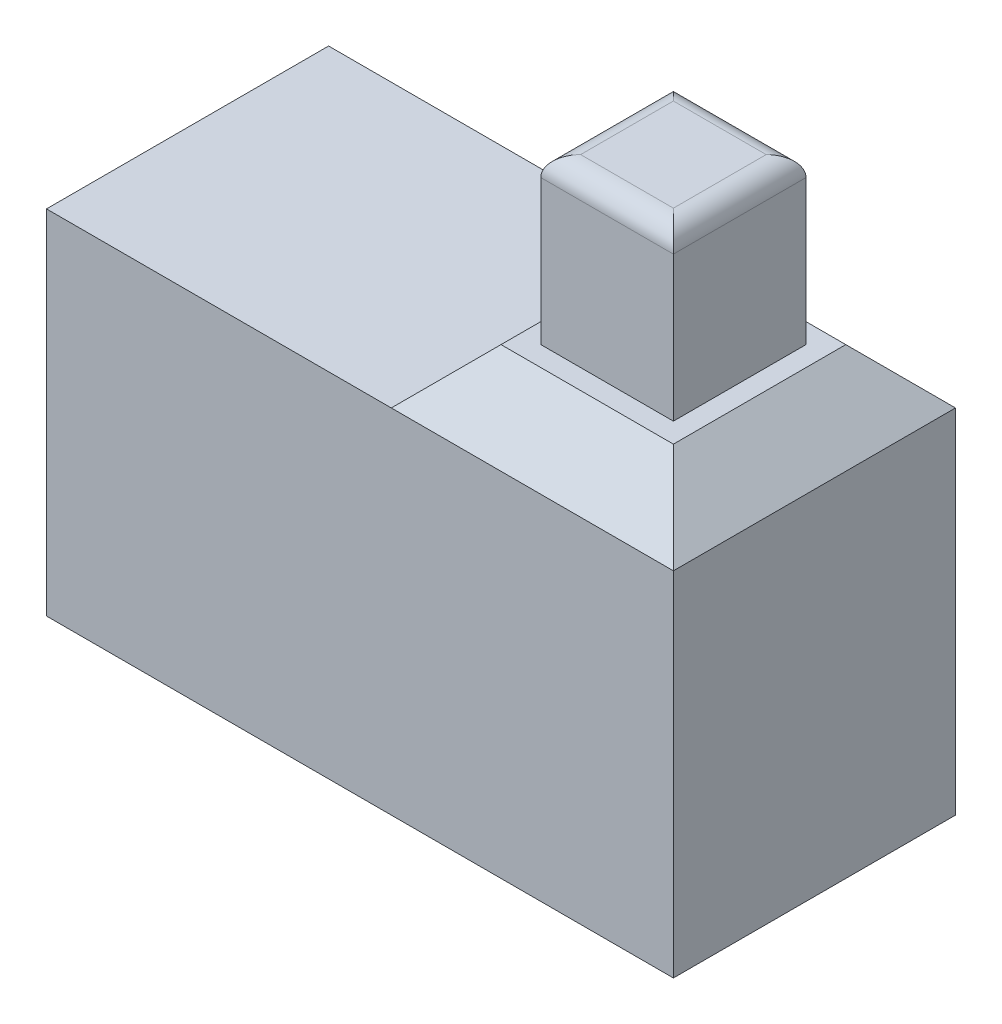
SolidWorks part; units mm, degrees
ref_plane "Front Plane" through (0, 0, 0) normal (0, 0, 1) x (1, 0, 0)
ref_plane "Top Plane" through (0, 0, 0) normal (0, 1, 0) x (1, 0, 0)
ref_plane "Right Plane" through (0, 0, 0) normal (1, 0, 0) x (0, 0, -1)
sketch "Sketch1" plane through (0, 0, 0) normal (0, 1, 0) x (1, 0, 0)
  line L1 (4, -1.8) -> (-4, -1.8)
  line L2 (4, -1.8) -> (4, 1.8)
  line L3 (4, 1.8) -> (-4, 1.8)
  line L4 (-4, -1.8) -> (-4, 1.8)
  line L5 (4, -1.8) -> (-4, 1.8) construction
  line L6 (4, 1.8) -> (-4, -1.8) construction
  point P0 (0, 0)
  dimension "D1" = 3.6
  dimension "D2" = 8
extrude "Boss-Extrude1" add sketch "Sketch1" along normal blind 4.5
sketch "Sketch2" plane through (0, 4.5, 0) normal (0, 1, 0) x (1, 0, 0)
  line L0 (-4, -1.8) -> (4, -1.8) construction
  line L1 (4, 1.8) -> (0.4, 1.8)
  line L2 (4, 1.8) -> (4, -1.8)
  line L3 (4, -1.8) -> (0.4, -1.8)
  line L4 (0.4, 1.8) -> (0.4, -1.8)
  dimension "D1" = 3.6
extrude "Boss-Extrude2" add sketch "Sketch2" along normal blind 0.7 draft 45
sketch "Sketch3" plane through (0, 5.2, 0) normal (0, 1, 0) x (1, 0, 0)
  line L8 (3.046, -0.846) -> (3.046, 0.846)
  line L9 (3.046, 0.846) -> (1.354, 0.846)
  line L10 (1.354, 0.846) -> (1.354, -0.846)
  line L11 (1.354, -0.846) -> (3.046, -0.846)
  line L12 (3.046, -0.846) -> (3.046, 0.846)
  line L13 (3.046, 0.846) -> (1.354, 0.846)
  line L14 (1.354, 0.846) -> (1.354, -0.846)
  line L15 (1.354, -0.846) -> (3.046, -0.846)
  dimension "D1" = 0.254
extrude "Boss-Extrude3" add sketch "Sketch3" along normal blind 2.1
fillet "Fillet1" radius 0.254 4 edges at (2.2, 7.3, -0.846) (1.354, 7.3, 0) (2.2, 7.3, 0.846) (3.046, 7.3, 0)
